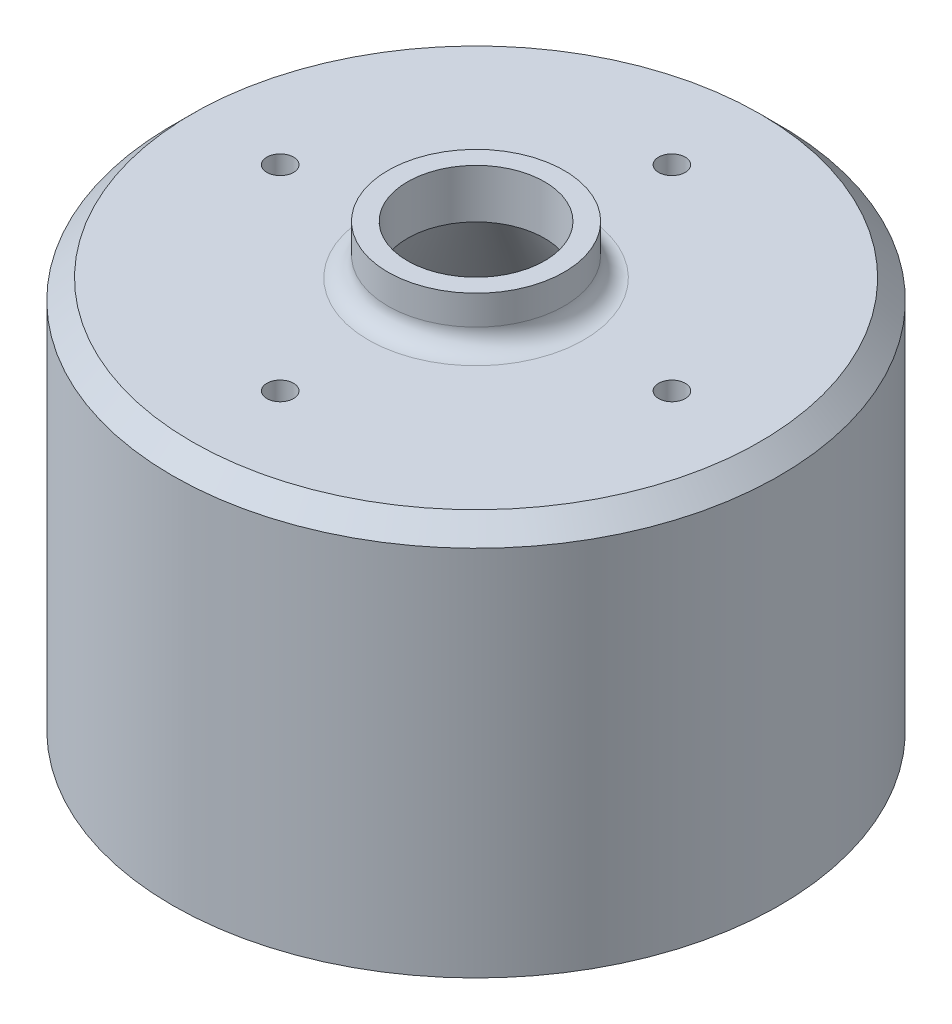
SolidWorks part; units mm, degrees
ref_plane "Front Plane" through (0, 0, 0) normal (0, 0, 1) x (1, 0, 0)
ref_plane "Top Plane" through (0, 0, 0) normal (0, 1, 0) x (1, 0, 0)
ref_plane "Right Plane" through (0, 0, 0) normal (1, 0, 0) x (0, 0, -1)
sketch "Sketch1" plane through (0, 0, 0) normal (0, 0, 1) x (1, 0, 0)
  line L0 (0, 33.4946) -> (0, -30.2908) construction
  line L1 (-8.89, 26.0055) -> (-8.89, 19.6555)
  line L2 (-8.89, 19.6555) -> (-38.2194, -31.1445)
  line L3 (-38.2194, -31.1445) -> (-39.37, -31.1445)
  line L4 (-39.37, -31.1445) -> (-39.37, 19.6555)
  line L5 (-39.37, 19.6555) -> (-11.43, 19.6555)
  line L6 (-11.43, 19.6555) -> (-11.43, 26.0055)
  line L7 (-11.43, 26.0055) -> (-8.89, 26.0055)
  dimension "D1" = 8.89
  dimension "D2" = 11.43
  dimension "D3" = 6.35
  dimension "D4" = 39.37
  dimension "D5" = 60
  dimension "D6" = 50.8
revolve "Revolve1" add sketch "Sketch1" angle 360 about L0
fillet "Fillet1" radius 2.54 1 edges at (0, 19.6555, 11.43)
chamfer "Chamfer1" distance 2.54 angle 45 1 edges at (0, 19.6555, 39.37)
hole_wizard "#8-32 Tapped Hole1" positions "Sketch2" profile "Sketch3" tap size "#8-32" standard "ANSI Inch"
sketch "Sketch2" plane through (0, 19.6555, 0) normal (0, 1, 0) x (1, 0, 0)
  point P0 (0, -25.4)
  point P2 (25.4, 0)
  point P4 (0, 25.4)
  point P6 (-25.4, 0)
  point P15 (21.7234, -12.7752)
  dimension "D1" = 25.4
  dimension "D2" = 25.4
  dimension "D3" = 25.4
  dimension "D4" = 25.4
sketch "Sketch3" plane through (0, 19.6555, 25.4) normal (1, 0, 0) x (0, 0, 1)
  line L0 (0, 0) -> (0, 11.7058)
  line L1 (0, 11.7058) -> (1.7272, 10.668)
  line L2 (1.7272, 10.668) -> (1.7272, 0)
  line L5 (1.7272, 0) -> (0, 0)
  line L10 (0, 11.7058) -> (-1.7272, 10.668) construction
  line L11 (0, -6.35) -> (0, 107.95) construction
  dimension "Tap Drill Dia." = 3.4544
  dimension "Tap Drill Depth" = 10.668
  dimension "Drill Angle" = 118
cosmetic thread "Hole Thread1"
cosmetic thread "Hole Thread2"
cosmetic thread "Hole Thread3"
cosmetic thread "Hole Thread4"
